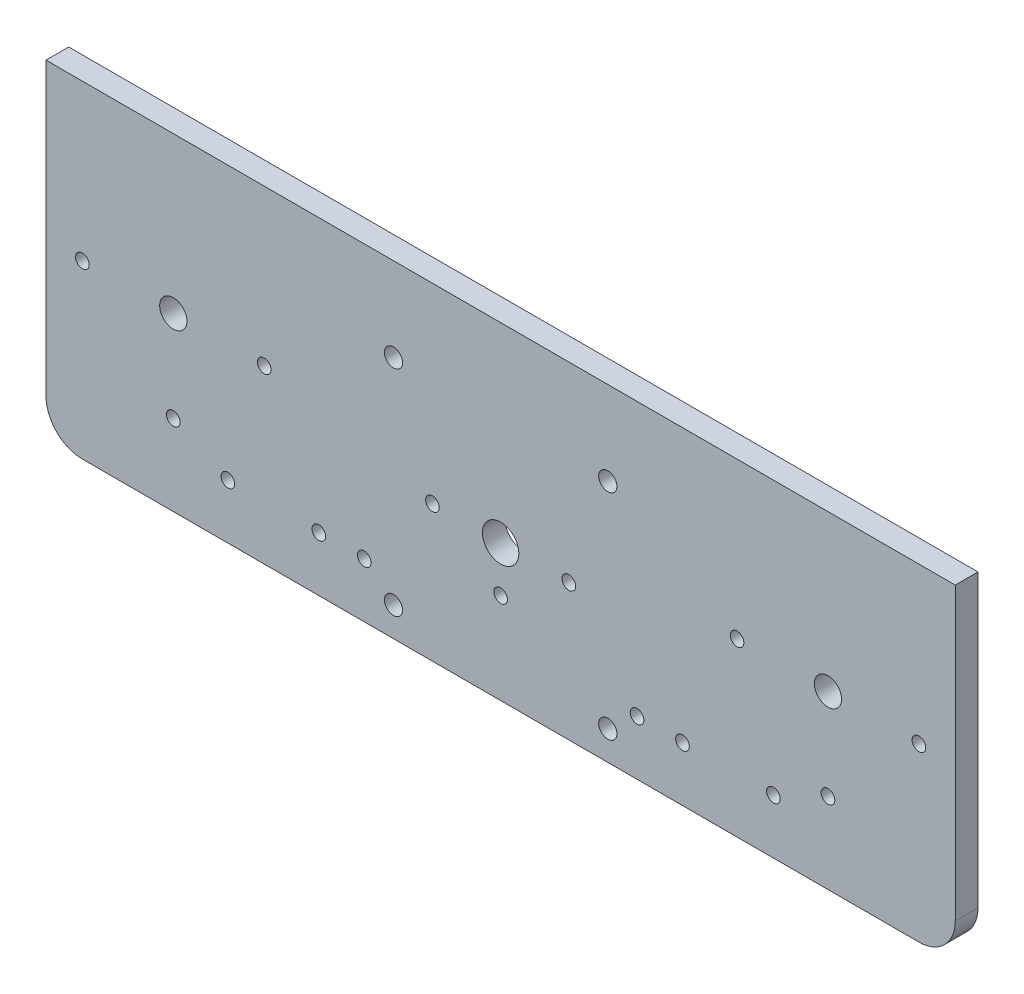
SolidWorks part; units mm, degrees
ref_plane "Alzado" through (0, 0, 0) normal (0, 0, 1) x (1, 0, 0)
ref_plane "Planta" through (0, 0, 0) normal (0, 1, 0) x (1, 0, 0)
ref_plane "Vista lateral" through (0, 0, 0) normal (1, 0, 0) x (0, 0, -1)
sketch "Croquis1" plane through (0, 0, 0) normal (0, 0, 1) x (1, 0, 0)
  line L0 (2.0685, -0.3273) -> (102.0685, -0.3273) construction
  line L1 (2.0685, -0.3273) -> (2.0685, -27.3273) construction
  line L2 (74.0685, -0.3273) -> (74.0685, -19.5773) construction
  line L3 (102.0685, -0.3273) -> (102.0685, -49.3273)
  line L4 (94.0685, -57.3273) -> (-89.9315, -57.3273)
  line L5 (2.0685, -57.3273) -> (2.0685, -27.3273) construction
  line L6 (2.0685, -0.3273) -> (2.0685, 14.6727) construction
  line L7 (-97.9315, 14.6727) -> (102.0685, 14.6727)
  line L8 (102.0685, 14.6727) -> (102.0685, -0.3273)
  line L9 (-97.9315, 14.6727) -> (-97.9315, -0.3273)
  line L10 (-97.9315, -0.3273) -> (-97.9315, -49.3273)
  line L11 (2.0685, -27.3273) -> (102.0685, -27.3273) construction
  line L12 (-21.5015, -50.8973) -> (25.6385, -50.8973) construction
  line L13 (-21.5015, -50.8973) -> (-21.5015, -3.7573) construction
  line L14 (-21.5015, -3.7573) -> (25.6385, -3.7573) construction
  line L15 (25.6385, -50.8973) -> (25.6385, -3.7573) construction
  line L16 (-21.5015, -50.8973) -> (25.6385, -3.7573) construction
  line L17 (-21.5015, -3.7573) -> (25.6385, -50.8973) construction
  circle A0 centre (2.0685, -27.3273) radius 4
  circle A1 centre (74.0685, -19.5773) radius 3
  circle A2 centre (-69.9315, -19.5773) radius 3
  circle A3 centre (74.0685, -39.5773) radius 1.5
  circle A4 centre (54.0685, -19.5773) radius 1.5
  circle A5 centre (94.0685, -19.5773) radius 1.5
  circle A6 centre (-69.9315, -19.5773) radius 3
  circle A7 centre (-69.9315, -39.5773) radius 1.5
  circle A8 centre (-89.9315, -19.5773) radius 1.5
  circle A9 centre (-49.9315, -19.5773) radius 1.5
  arc A10 (102.0685, -49.3273) -> (94.0685, -57.3273) centre (94.0685, -49.3273) cw
  arc A11 (-97.9315, -49.3273) -> (-89.9315, -57.3273) centre (-89.9315, -49.3273) ccw
  circle A12 centre (42.0685, -45.3273) radius 1.5
  circle A13 centre (62.0685, -45.3273) radius 1.5
  circle A14 centre (-57.9315, -45.3273) radius 1.5
  circle A15 centre (-37.9315, -45.3273) radius 1.5
  circle A16 centre (-12.9315, -27.3273) radius 1.5
  circle A17 centre (17.0685, -27.3273) radius 1.5
  circle A18 centre (2.0685, -37.3273) radius 1.5
  circle A19 centre (-21.5015, -3.7573) radius 2
  circle A20 centre (25.6385, -3.7573) radius 2
  circle A21 centre (25.6385, -50.8973) radius 2
  circle A22 centre (-21.5015, -50.8973) radius 2
  circle A23 centre (32.0685, -45.3273) radius 1.5
  circle A24 centre (-27.9315, -45.3273) radius 1.5
  point P60 (0, 0)
  dimension "D4" = 8
  dimension "D5" = 6
  dimension "D10" = 3
  dimension "D11" = 3
  dimension "D13" = 8
  dimension "D14" = 3
  dimension "D15" = 3
  dimension "D19" = 3
  dimension "D21" = 3
  dimension "D24" = 4
  dimension "D25" = 3
  dimension "D1" = 19.25
  dimension "D2" = 27
  dimension "D3" = 72
  dimension "D6" = 100
  dimension "D7" = 47.14
  dimension "D8" = 20
  dimension "D9" = 20
  dimension "D12" = 15
  dimension "D16" = 20
  dimension "D17" = 40
  dimension "D18" = 12
  dimension "D20" = 15
  dimension "D22" = 10
  dimension "D23" = 47.14
  dimension "D26" = 30
extrude "Saliente-Extruir1" add sketch "Croquis1" along normal blind 5 contours L10 A11 L4 A10 L3 L8 L7 L9 A20 A19 A18 A15 A7 A2 A1 A0 A3 A4 A5 A8 A9 A12 A13 A14 A16 A17 A21 A22
